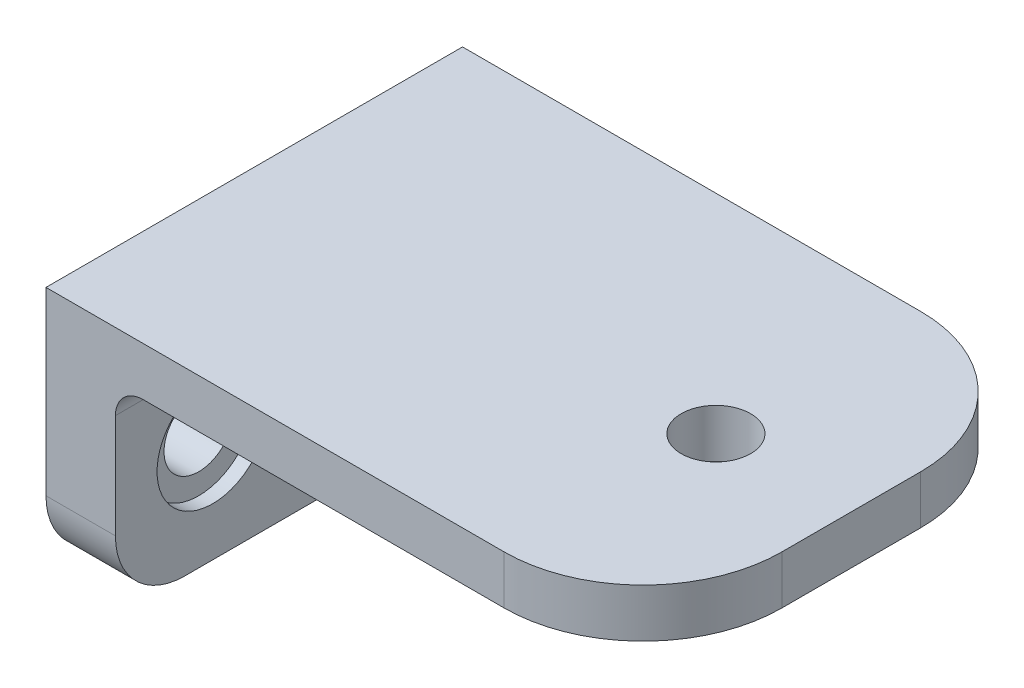
SolidWorks part; units mm, degrees
ref_plane "Front Plane" through (0, 0, 0) normal (0, 0, 1) x (1, 0, 0)
ref_plane "Top Plane" through (0, 0, 0) normal (0, 1, 0) x (1, 0, 0)
ref_plane "Right Plane" through (0, 0, 0) normal (1, 0, 0) x (0, 0, -1)
sketch "Sketch1" plane through (0, 0, 0) normal (0, 1, 0) x (1, 0, 0)
  line L1 (19, -15) -> (-19, -15)
  line L2 (19, -15) -> (19, 15)
  line L3 (19, 15) -> (-19, 15)
  line L4 (-19, -15) -> (-19, 15)
  line L5 (19, -15) -> (-19, 15) construction
  line L6 (19, 15) -> (-19, -15) construction
  point P0 (0, 0)
  dimension "D1" = 38
  dimension "D2" = 30
extrude "Boss-Extrude1" add sketch "Sketch1" along normal blind 3.5
sketch "Sketch2" plane through (-19, 0, 0) normal (-1, 0, 0) x (0, 0, 1)
  line L0 (15, 3.5) -> (15, 0) construction
  line L1 (-15, 3.5) -> (15, 3.5)
  line L2 (-15, 3.5) -> (-15, -14.5)
  line L3 (-15, -14.5) -> (15, -14.5)
  line L4 (15, 3.5) -> (15, -14.5)
  dimension "D1" = 0
  dimension "D2" = 18
extrude "Boss-Extrude2" add sketch "Sketch2" along normal blind 5
sketch "Sketch3" plane through (-19, 0, 0) normal (1, 0, 0) x (0, 0, -1)
  line L0 (15, -14.5) -> (-15, -14.5) construction
  circle A0 centre (-8, -7) radius 4
  circle A1 centre (8, -7) radius 4
  point P6 (0, -14.5)
  dimension "D1" = 8
  dimension "D2" = 8
  dimension "D3" = 7.5
  dimension "D4" = 7.5
extrude "Cut-Extrude1" cut sketch "Sketch3" against normal blind 1
sketch "Sketch4" plane through (-20, 0, 0) normal (1, 0, 0) x (0, 0, -1)
  circle A0 centre (-8, -7) radius 2.5
  circle A1 centre (8, -7) radius 2.5
extrude "Cut-Extrude2" cut sketch "Sketch4" against normal blind 5
sketch "Sketch5" plane through (0, 3.5, 0) normal (0, 1, 0) x (1, 0, 0)
  line L0 (-24, -15) -> (-24, 15) construction
  circle A0 centre (9.25, 0) radius 2.5
  dimension "D1" = 33.25
extrude "Cut-Extrude3" cut sketch "Sketch5" against normal blind 5
fillet "Fillet1" radius 10 2 edges at (19, 1.75, -15) (19, 1.75, 15)
fillet "Fillet2" radius 2 1 edges at (-19, 0, 0)
fillet "Fillet3" radius 5 2 edges at (-21.5, -14.5, -15) (-21.5, -14.5, 15)
